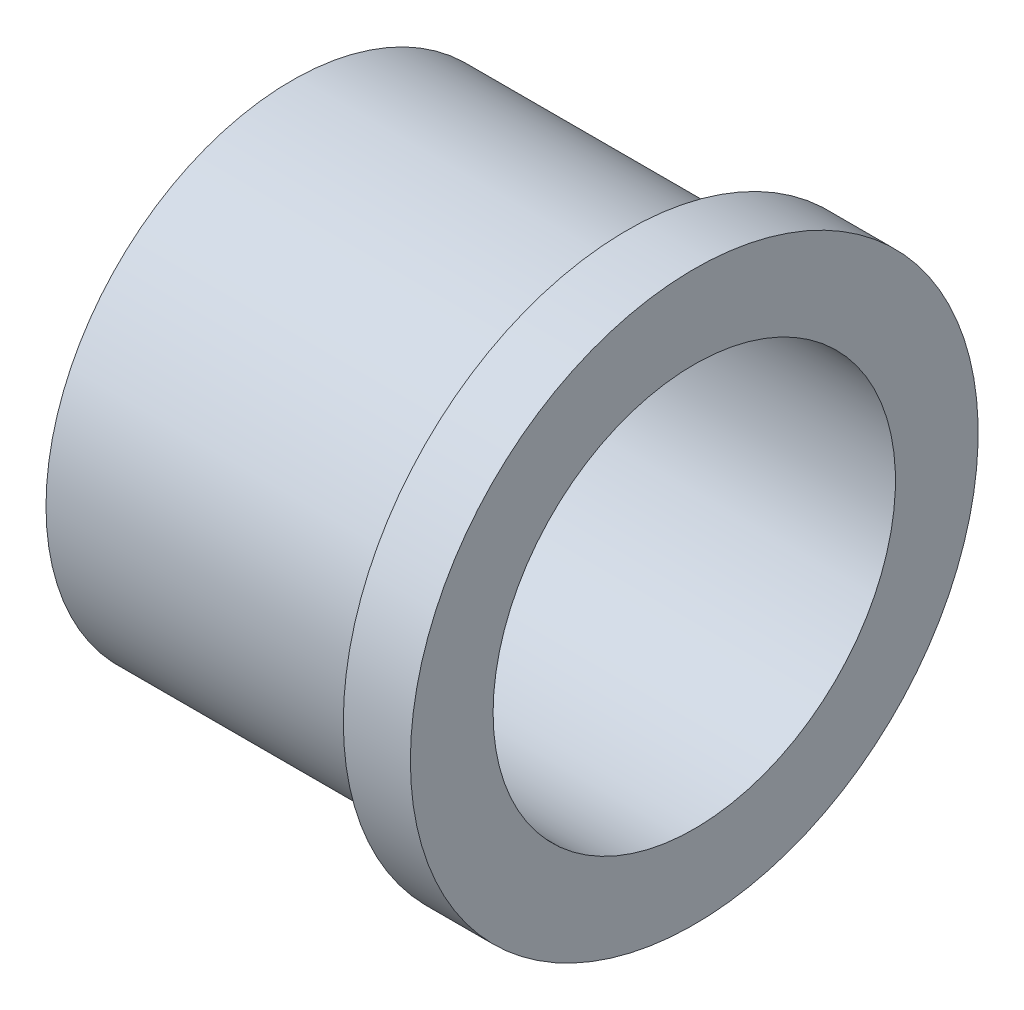
SolidWorks part; units mm, degrees
material "Brass"
ref_plane "Front Plane" through (0, 0, 0) normal (0, 0, 1) x (1, 0, 0)
ref_plane "Top Plane" through (0, 0, 0) normal (0, 1, 0) x (1, 0, 0)
ref_plane "Right Plane" through (0, 0, 0) normal (1, 0, 0) x (0, 0, -1)
sketch "Sketch1" plane through (0, 0, 0) normal (0, 1, 0) x (1, 0, 0)
  line L0 (0, 12.7) -> (0, 11)
  line L1 (0, 11) -> (-15, 11)
  line L2 (-15, 11) -> (-15, 9)
  line L3 (-15, 9) -> (3, 9)
  line L4 (3, 9) -> (3, 12.7)
  line L5 (3, 12.7) -> (0, 12.7)
  line L6 (-93.5891, 0) -> (54.1717, 0) construction
  dimension "D1" = 25.4
  dimension "D2" = 18
  dimension "D3" = 3
  dimension "D4" = 15
  dimension "D5" = 2
revolve "Revolve1" add sketch "Sketch1" angle 360 about L6
